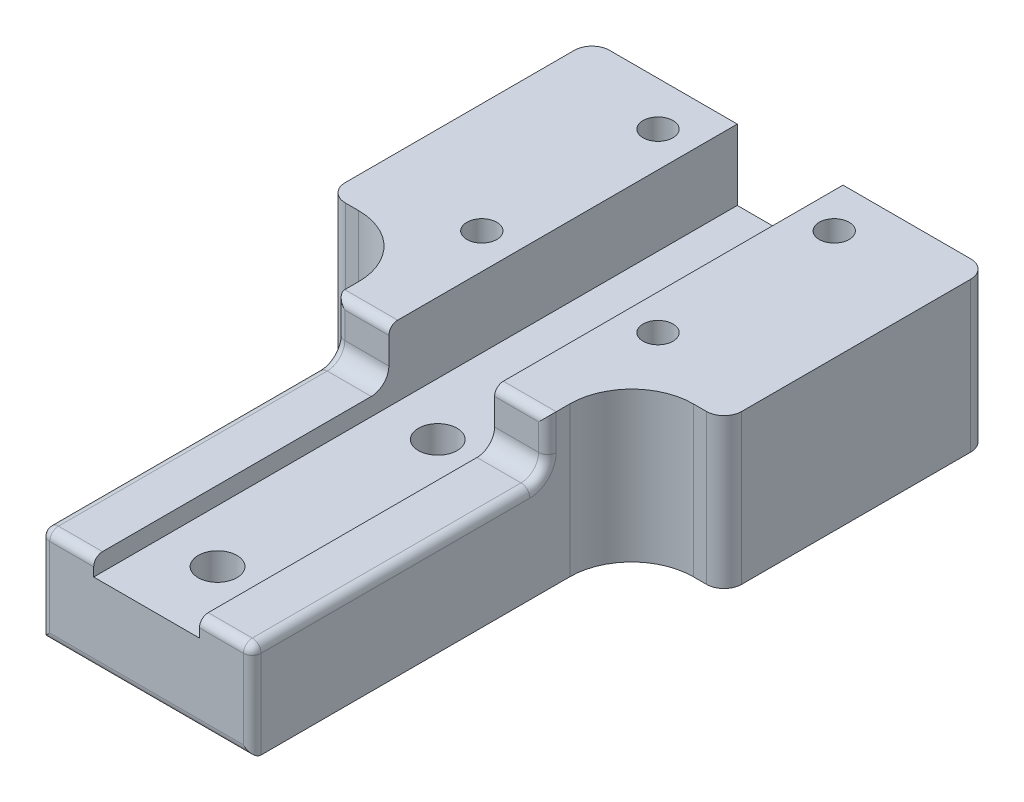
SolidWorks part; units mm, degrees
ref_plane "Front Plane" through (0, 0, 0) normal (0, 0, 1) x (1, 0, 0)
ref_plane "Top Plane" through (0, 0, 0) normal (0, 1, 0) x (1, 0, 0)
ref_plane "Right Plane" through (0, 0, 0) normal (1, 0, 0) x (0, 0, -1)
sketch "Sketch1" plane through (0, 0, 0) normal (0, 1, 0) x (1, 0, 0)
  line L0 (0, -55) -> (0, 55) construction
  line L1 (-22.5, 15) -> (22.5, 15)
  line L2 (-22.5, 15) -> (-22.5, -15)
  line L3 (-22.5, -15) -> (22.5, -15)
  line L4 (22.5, 15) -> (22.5, -15)
  line L5 (-22.5, 15) -> (22.5, -15) construction
  line L6 (-22.5, -15) -> (22.5, 15) construction
  line L7 (-10, 10) -> (10, 10)
  line L8 (-10, 10) -> (-10, -10) construction
  line L9 (-10, -10) -> (10, -10) construction
  line L10 (10, 10) -> (10, -10) construction
  line L11 (-10, 10) -> (10, -10) construction
  line L12 (-10, -10) -> (10, 10) construction
  line L13 (-12, -15) -> (12, -15)
  line L14 (-12, -15) -> (-12, -58.0584)
  line L15 (-12, -58.0584) -> (12, -58.0584)
  line L16 (12, -15) -> (12, -58.0584)
  line L17 (0, -1000) -> (0, 49000) construction
  circle A0 centre (-10, 10) radius 1.7
  circle A1 centre (10, 10) radius 1.7
  circle A2 centre (10, -10) radius 1.7
  circle A3 centre (-10, -10) radius 1.7
  circle A4 centre (0, -25) radius 2.2
  circle A5 centre (0, -50) radius 2.2
  point P0 (0, 0)
  point P6 (0, 0)
  dimension "D1" = 3.4
  dimension "D9" = 40
  dimension "D6" = 25
  dimension "D8" = 4.4
  dimension "D2" = 45
  dimension "D3" = 20
  dimension "D4" = 20
  dimension "D5" = 30
  dimension "D7" = 24
extrude "Boss-Extrude2" add sketch "Sketch1" against normal blind 17
sketch "Sketch5" plane through (0, 0, 0) normal (0, 1, 0) x (1, 0, 0)
  line L0 (0, -55) -> (0, 55) construction
  line L1 (-6, 33.5348) -> (6, 33.5348)
  line L2 (-6, 33.5348) -> (-6, -66.4652)
  line L3 (-6, -66.4652) -> (6, -66.4652)
  line L4 (6, 33.5348) -> (6, -66.4652)
  line L5 (-6, 33.5348) -> (6, -66.4652) construction
  line L6 (-6, -66.4652) -> (6, 33.5348) construction
  point P0 (0, -16.4652)
  dimension "D1" = 12
  dimension "D2" = 100
extrude "Cut-Extrude1" cut sketch "Sketch5" against normal blind 8
ref_plane "Plane12" through (0, -6, 0) normal (0, 1, 0) x (1, 0, 0)
sketch "Sketch7" plane through (0, -6, 0) normal (0, 1, 0) x (1, 0, 0)
  line L1 (-15.6584, -24.5529) -> (14.0386, -24.5529)
  line L2 (-15.6584, -24.5529) -> (-15.6584, -59.5414)
  line L3 (-15.6584, -59.5414) -> (14.0386, -59.5414)
  line L4 (14.0386, -24.5529) -> (14.0386, -59.5414)
  line L5 (-0.8099, -59.5414) -> (-0.8099, -24.5529) construction
  line L6 (-15.6584, -42.0471) -> (14.0386, -42.0471) construction
  point P192 (-0.8099, -42.0471)
extrude "Cut-Extrude2" cut sketch "Sketch7" along normal through all
fillet "Fillet1" radius 7 2 edges at (-12, -8.5, 15) (12, -8.5, 15)
fillet "Fillet6" radius 2 6 edges at (-9, -6, 24.5529) (9, -6, 24.5529) (-22.5, -8.5, 15) (-22.5, -8.5, -15) (22.5, -8.5, -15) (22.5, -8.5, 15)
fillet "Fillet7" radius 1 13 edges at (-12, -2, 24.5529) (-12, -5.4142, 25.1387) (12, -2, 24.5529) (12, -5.4142, 25.1387) (-12, -6, 42.3056) (-9, -6, 58.0584) (9, -6, 58.0584) (12, -6, 42.3056) (0, -17, 58.0584) (-12, -11.5, 58.0584) (12, -11.5, 58.0584) (-9, 0, 24.5529) (9, 0, 24.5529)
